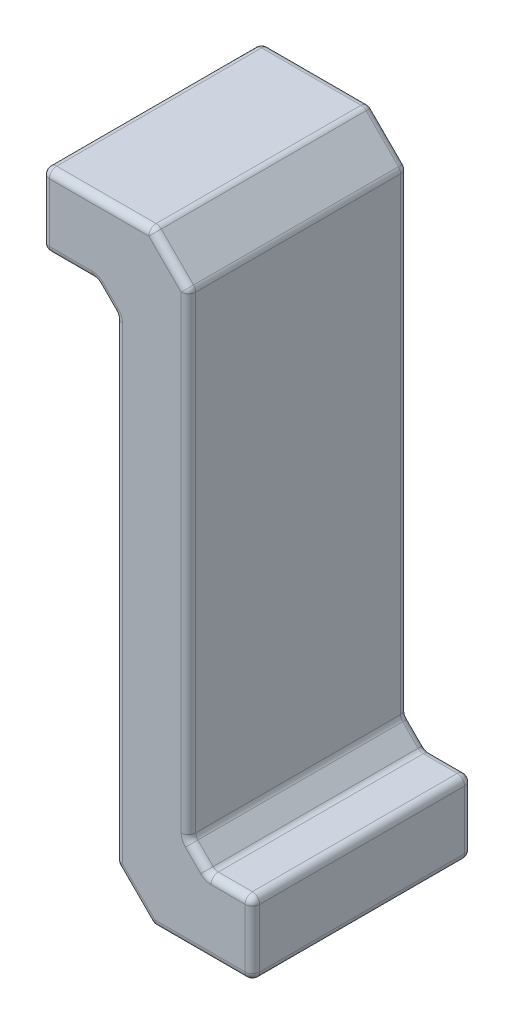
SolidWorks part; units mm, degrees
ref_plane "Front Plane" through (0, 0, 0) normal (0, 0, 1) x (1, 0, 0)
ref_plane "Top Plane" through (0, 0, 0) normal (0, 1, 0) x (1, 0, 0)
ref_plane "Right Plane" through (0, 0, 0) normal (1, 0, 0) x (0, 0, -1)
sketch "Sketch1" plane through (0, 0, 0) normal (1, 0, 0) x (0, 0, -1)
  line L1 (0, 0) -> (12, 0)
  line L2 (0, 0) -> (0, 4)
  line L3 (0, 4) -> (12, 4)
  line L4 (12, 0) -> (12, 4)
  dimension "D1" = 12
  dimension "D2" = 4
extrude "Boss-Extrude1" add sketch "Sketch1" along normal blind 8
sketch "Sketch2" plane through (0, 0, 0) normal (0, -1, 0) x (1, 0, 0)
  line L0 (8, 0) -> (0, 0) construction
  line L1 (8, -12) -> (4, -12)
  line L2 (8, -12) -> (8, 0)
  line L3 (8, 0) -> (4, 0)
  line L4 (4, -12) -> (4, 0)
  dimension "D1" = 4
extrude "Boss-Extrude2" add sketch "Sketch2" along normal blind 25
sketch "Sketch3" plane through (0, -25, 0) normal (0, -1, 0) x (1, 0, 0)
  line L0 (8, 0) -> (4, 0) construction
  line L1 (4, -12) -> (11.5, -12)
  line L2 (4, -12) -> (4, 0)
  line L3 (4, 0) -> (11.5, 0)
  line L4 (11.5, -12) -> (11.5, 0)
  dimension "D1" = 7.5
extrude "Boss-Extrude3" add sketch "Sketch3" along normal blind 4
chamfer "Chamfer1" distance 2 angle 45 2 edges at (4, -29, -6) (8, 4, -6)
sketch "Sketch4" plane through (0, 0, -12) normal (0, 0, -1) x (-1, 0, 0)
  line L0 (-2.9289, 0) -> (-4, -1.0711)
  line L1 (-4, 0) -> (0, 0) construction
  line L2 (-4, -27) -> (-4, 0) construction
  line L3 (-6, 4) -> (-8, 2) construction
  dimension "D1" = 5
rib "Rib1" sketch "Sketch4" sketch "Sketch4" thickness 12 extrusion direction parallel to sketch draft on no parameters "D1"=12
sketch "Sketch5" plane through (0, 0, 0) normal (0, 0, 1) x (1, 0, 0)
  line L0 (8, -23.9289) -> (9.0711, -25)
  line L1 (8, 2) -> (8, -25) construction
  line L2 (11.5, -25) -> (8, -25) construction
  line L4 (4, -27) -> (6, -29) construction
  dimension "D1" = 5
rib "Rib2" sketch "Sketch5" sketch "Sketch5" thickness 12 extrusion direction parallel to sketch draft on no parameters "D1"=12
sketch "Sketch7" plane through (0, 0, 0) normal (-1, 0, 0) x (0, 0, 1)
  line L0 (-12, 0) -> (-12, 4) construction
  line L1 (-12, 4) -> (0, 4) construction
  circle A0 centre (-6, 2) radius 1
  point P5 (-12, 2)
  point P9 (-6, 4)
  dimension "D1" = 2
extrude "Cut-Extrude2" cut sketch "Sketch7" against normal blind 4
fillet "Fillet1" radius 0.4 36 edges at (6, -29, -6) (0, 0, -6) (2.9289, 0, -6) (4, -27, -6) (4, -1.0711, -6) (4, -14.0355, 0) (3.4645, -0.5355, -12) (3.4645, -0.5355, 0) (1.4645, 0, 0) (0, 2, 0) (8.5355, -24.4645, 0) (8.5355, -24.4645, -12) (8.75, -29, 0) (5, -28, 0) (11.5, -29, -6) (11.5, -27, 0) (11.5, -25, -6) (10.2855, -25, 0) (9.0711, -25, -6) (5, -28, -12) (8.75, -29, -12) (11.5, -27, -12) (10.2855, -25, -12) (0, 2, -12) (1.4645, 0, -12) (4, -14.0355, -12) (0, 4, -6) (3, 4, -12) (3, 4, 0) (7, 3, 0) (6, 4, -6) (7, 3, -12) (8, 2, -6) (8, -10.9645, -12) (8, -23.9289, -6) (8, -10.9645, 0)
